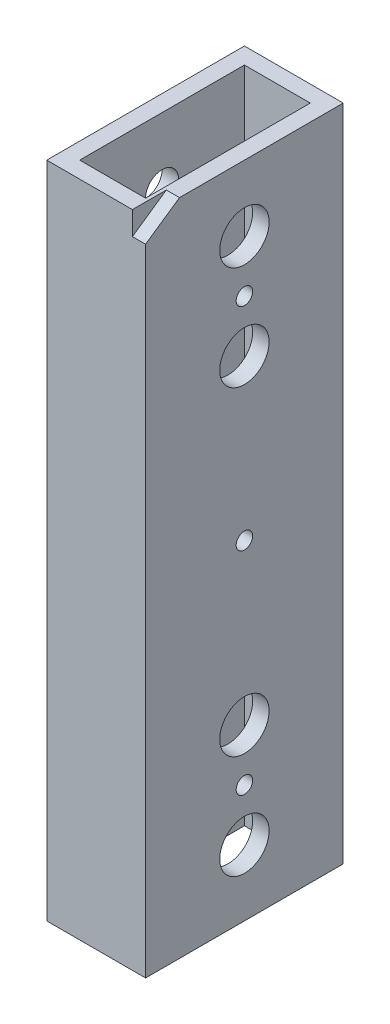
SolidWorks part; units mm, degrees
ref_plane "Front" through (0, 0, 0) normal (0, 0, 1) x (1, 0, 0)
ref_plane "Top" through (0, 0, 0) normal (0, 1, 0) x (1, 0, 0)
ref_plane "Right" through (0, 0, 0) normal (1, 0, 0) x (0, 0, -1)
sketch "Sketch1" plane through (0, 0, 0) normal (0, 1, 0) x (1, 0, 0)
  line L0 (3.175, 3.175) -> (15.875, 3.175)
  line L1 (0, 0) -> (19.05, 0)
  line L2 (0, 0) -> (0, 38.1)
  line L3 (0, 38.1) -> (19.05, 38.1)
  line L4 (19.05, 0) -> (19.05, 38.1)
  line L5 (15.875, 3.175) -> (15.875, 34.925)
  line L6 (3.175, 34.925) -> (15.875, 34.925)
  line L7 (3.175, 3.175) -> (3.175, 34.925)
  dimension "D1" = 38.1
  dimension "D2" = 19.05
  dimension "D3" = 3.175
extrude "Boss-Extrude1" add sketch "Sketch1" along normal blind 127
sketch "Sketch2" plane through (19.05, 0, 0) normal (1, 0, 0) x (0, 0, -1)
  line L0 (19.05, 0) -> (19.05, 12.7) construction
  line L1 (0, 0) -> (38.1, 0) construction
  line L2 (19.05, 12.7) -> (19.05, 32.7) construction
  line L3 (0, 63.5) -> (38.1, 63.5) construction
  line L4 (0, 127) -> (0, 0) construction
  line L5 (38.1, 127) -> (38.1, 0) construction
  line L6 (19.05, 114.3) -> (19.05, 94.3) construction
  circle A0 centre (19.05, 12.7) radius 3.175
  circle A1 centre (19.05, 32.7) radius 3.175
  circle A2 centre (19.05, 94.3) radius 3.175
  circle A3 centre (19.05, 114.3) radius 3.175
  dimension "D2" = 6.35
  dimension "D1" = 12.7
  dimension "D3" = 20
extrude "Cut-Extrude1" cut sketch "Sketch2" against normal through all
sketch "Sketch3" plane through (19.05, 0, 0) normal (1, 0, 0) x (0, 0, -1)
  circle A0 centre (19.05, 114.3) radius 4.7625
  circle A1 centre (19.05, 94.3) radius 4.7625
  circle A2 centre (19.05, 32.7) radius 4.7625
  circle A4 centre (19.05, 12.7) radius 4.7625
  circle A5 centre (19.05, 32.7) radius 3.175 construction
  circle A6 centre (19.05, 12.7) radius 3.175 construction
  circle A7 centre (19.05, 94.3) radius 3.175 construction
  circle A8 centre (19.05, 114.3) radius 3.175 construction
  dimension "D1" = 9.525
extrude "Cut-Extrude2" cut sketch "Sketch3" against normal up to next
sketch "Sketch4" plane through (19.05, 0, 0) normal (1, 0, 0) x (0, 0, -1)
  line L0 (19.05, 27.9375) -> (19.05, 17.4625) construction
  line L1 (0, 63.5) -> (38.1, 63.5) construction
  line L2 (0, 127) -> (0, 0) construction
  line L3 (38.1, 127) -> (38.1, 0) construction
  circle A0 centre (19.05, 32.7) radius 4.7625 construction
  circle A1 centre (19.05, 12.7) radius 4.7625 construction
  circle A2 centre (19.05, 22.7) radius 1.5875
  circle A3 centre (19.05, 63.5) radius 1.5875
  circle A4 centre (19.05, 104.3) radius 1.5875
  dimension "D1" = 3.175
  dimension "D2" = 40.8
extrude "UChan_Mount" cut sketch "Sketch4" against normal through all
sketch "Sketch5" plane through (0, 0, 0) normal (-1, 0, 0) x (0, 0, 1)
  circle A0 centre (-19.05, 104.3) radius 4.7625
  circle A1 centre (-19.05, 63.5) radius 4.7625
  circle A2 centre (-19.05, 22.7) radius 4.7625
  circle A3 centre (-19.05, 22.7) radius 1.5875 construction
  circle A4 centre (-19.05, 63.5) radius 1.5875 construction
  circle A5 centre (-19.05, 104.3) radius 1.5875 construction
  dimension "D1" = 9.525
extrude "Cut-Extrude4" cut sketch "Sketch5" against normal up to next
ref_plane "Mid_Plane" through (0, 0, -19.05) normal (0, 0, -1) x (-1, 0, 0)
sketch "Sketch6" plane through (19.05, 0, 0) normal (1, 0, 0) x (0, 0, -1)
  line L0 (0, 127) -> (6.5374, 127)
  line L1 (0, 127) -> (38.1, 127) construction
  line L2 (6.5374, 127) -> (0, 122.4876)
  line L3 (0, 127) -> (0, 0) construction
  line L4 (0, 122.4876) -> (0, 127)
extrude "Cut-Extrude5" cut sketch "Sketch6" against normal blind 2.54
